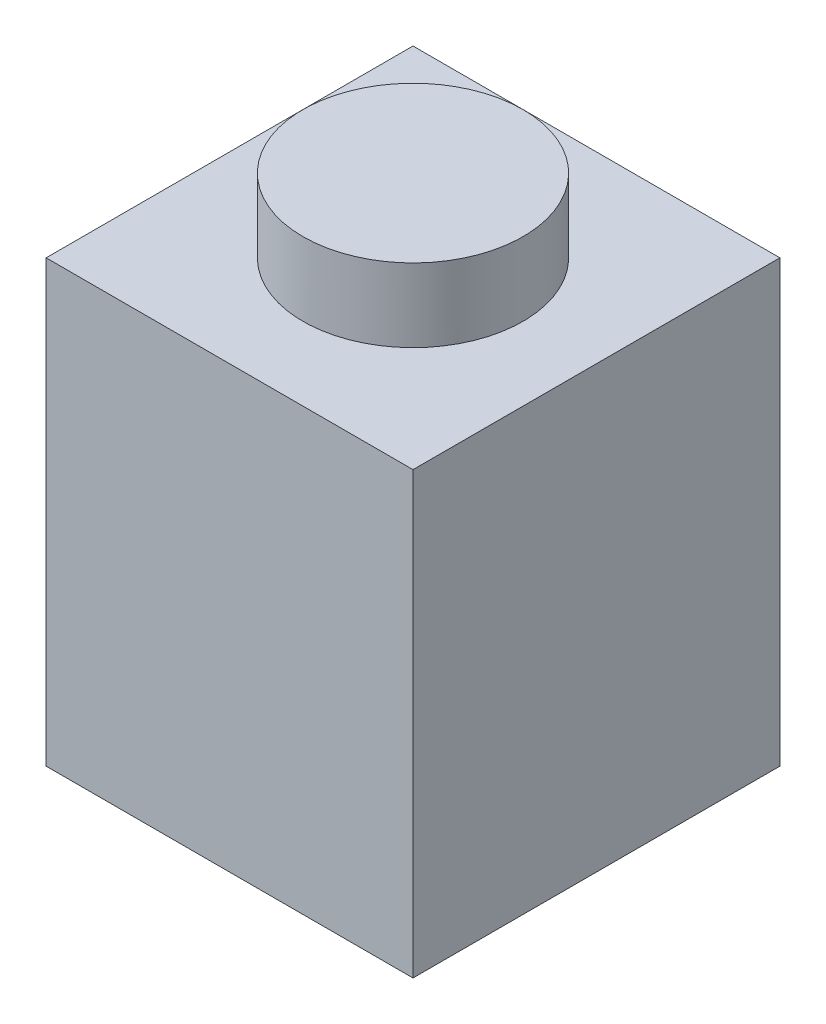
SolidWorks part; units mm, degrees
ref_plane "Front Plane" through (0, 0, 0) normal (0, 0, 1) x (1, 0, 0)
ref_plane "Top Plane" through (0, 0, 0) normal (0, 1, 0) x (1, 0, 0)
ref_plane "Right Plane" through (0, 0, 0) normal (1, 0, 0) x (0, 0, -1)
sketch "Sketch1" plane through (0, 0, 0) normal (0, 1, 0) x (1, 0, 0)
  line L1 (0, 0) -> (5, 0)
  line L2 (0, 0) -> (0, 5)
  line L3 (0, 5) -> (5, 5)
  line L4 (5, 0) -> (5, 5)
  line L5 (1, 4) -> (4, 4)
  line L6 (1, 4) -> (1, 1)
  line L7 (1, 1) -> (4, 1)
  line L8 (4, 4) -> (4, 1)
  point P9 (2.5, 4)
  point P10 (2.5, 5)
  point P11 (4, 2.5)
  point P12 (5, 2.5)
  dimension "D1" = 5
  dimension "D2" = 3
extrude "Boss-Extrude1" add sketch "Sketch1" along normal blind 6
sketch "Sketch2" plane through (0, 0, -4) normal (0, 0, 1) x (1, 0, 0)
  line L0 (4, 6) -> (4, 0) construction
  line L1 (1, 6) -> (4, 6)
  line L2 (1, 6) -> (1, 5)
  line L3 (1, 5) -> (4, 5)
  line L4 (4, 6) -> (4, 5)
  dimension "D1" = 1
extrude "Boss-Extrude2" add sketch "Sketch2" along normal up to next
sketch "Sketch3" plane through (0, 6, 0) normal (0, 1, 0) x (1, 0, 0)
  line L0 (0, 5) -> (5, 0)
  line L1 (0, 0) -> (5, 5)
  circle A0 centre (2.5, 2.5) radius 1.5
  dimension "D1" = 3
extrude "Boss-Extrude3" add sketch "Sketch3" along normal blind 1 contours L1 A0 L0 | L0 A0 L1 | L1 A0 L0 | L0 A0 L1
sketch "Sketch4" plane through (0, 5, 0) normal (0, -1, 0) x (1, 0, 0)
  line L1 (4, -1) -> (1, -1)
  line L2 (4, -1) -> (4, -4)
  line L3 (4, -4) -> (1, -4)
  line L4 (1, -1) -> (1, -4)
  circle A0 centre (2.5, -2.5) radius 0.75
  point P8 (0, 0)
  point P9 (4, -2.5)
  point P10 (0, 0)
  point P11 (2.5, -1)
  dimension "D1" = 1.5
extrude "Cut-Extrude2" cut sketch "Sketch4" against normal blind 1 contours A0
